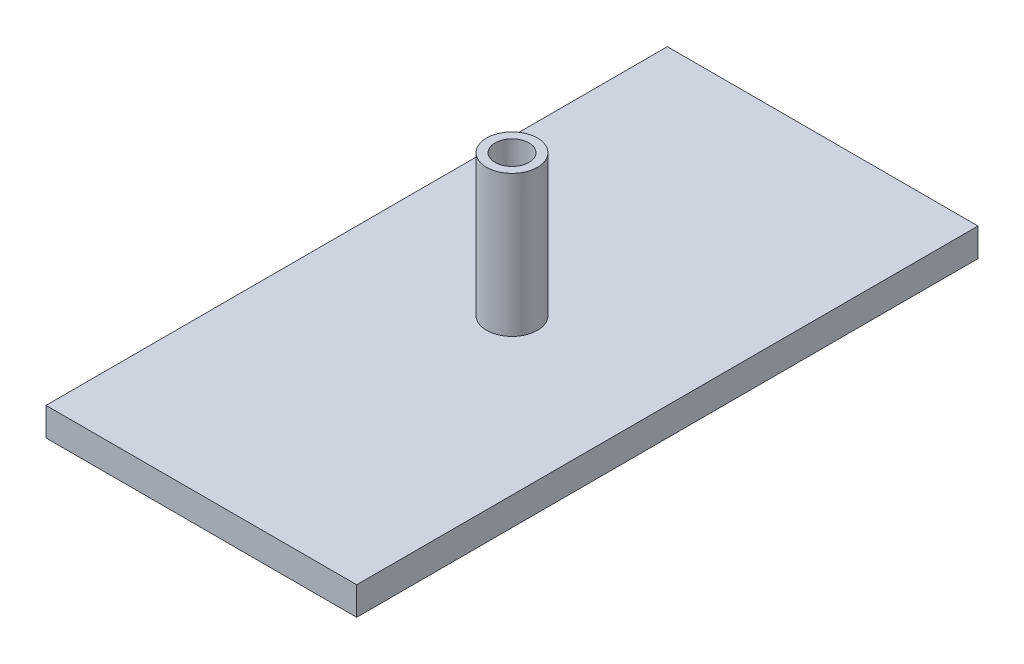
SolidWorks part; units mm, degrees
ref_plane "Front Plane" through (0, 0, 0) normal (0, 0, 1) x (1, 0, 0)
ref_plane "Top Plane" through (0, 0, 0) normal (0, 1, 0) x (1, 0, 0)
ref_plane "Right Plane" through (0, 0, 0) normal (1, 0, 0) x (0, 0, -1)
sketch "Sketch1" plane through (0, 0, 0) normal (0, 1, 0) x (1, 0, 0)
  line L1 (0, 0) -> (55, 0)
  line L2 (0, 0) -> (0, 110)
  line L3 (0, 110) -> (55, 110)
  line L4 (55, 0) -> (55, 110)
extrude "Boss-Extrude3" add sketch "Sketch1" along normal blind 5 contours L1 L4 L3 L2
sketch "Sketch3" plane through (0, 5, 0) normal (0, 1, 0) x (1, 0, 0)
  circle A0 centre (27.5, 55) radius 4.5
  point P2 (0, 0)
  point P3 (0, 0)
  point P4 (0, 0)
  point P7 (0, 0)
extrude "Boss-Extrude4" add sketch "Sketch3" along normal blind 25
sketch "Sketch4" plane through (0, 30, 0) normal (0, 1, 0) x (1, 0, 0)
  circle A0 centre (27.5, 55) radius 3
  point P3 (0, 0)
extrude "Cut-Extrude1" cut sketch "Sketch4" against normal blind 20
